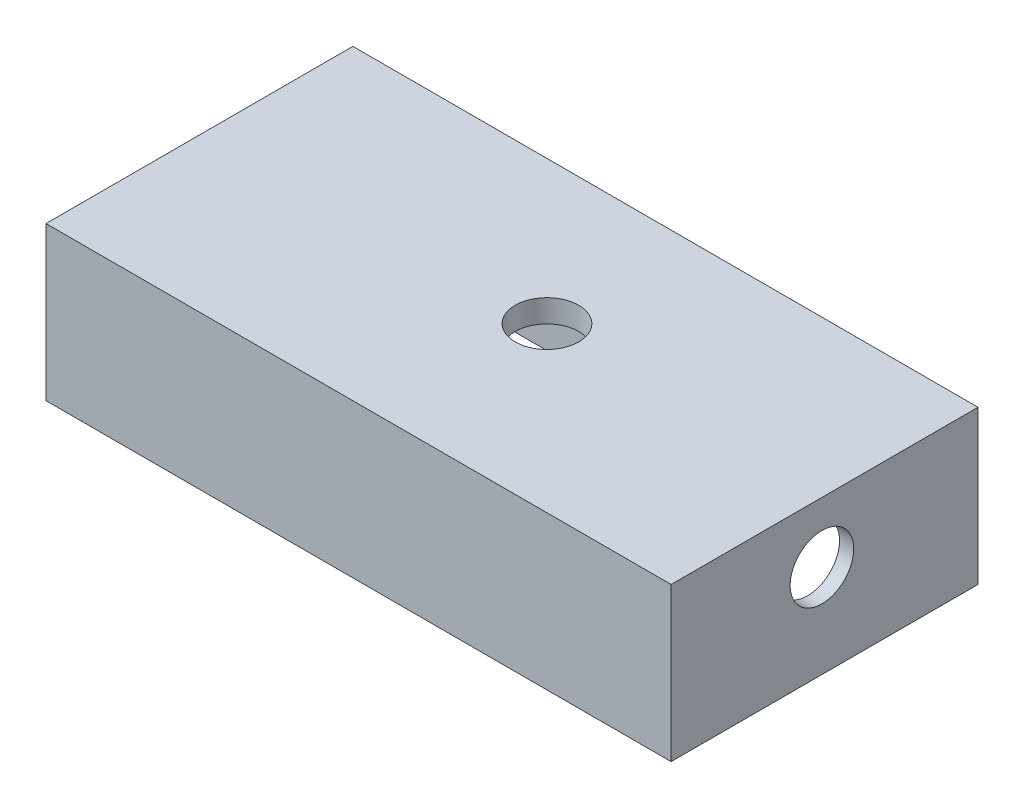
SolidWorks part; units mm, degrees
material "6061 Alloy"
ref_plane "Front Plane" through (0, 0, 0) normal (0, 0, 1) x (1, 0, 0)
ref_plane "Top Plane" through (0, 0, 0) normal (0, 1, 0) x (1, 0, 0)
ref_plane "Right Plane" through (0, 0, 0) normal (1, 0, 0) x (0, 0, -1)
sketch "Sketch1" plane through (0, 0, 0) normal (0, 1, 0) x (1, 0, 0)
  line L1 (-174.625, -85.725) -> (174.625, -85.725)
  line L2 (-174.625, -85.725) -> (-174.625, 85.725)
  line L3 (-174.625, 85.725) -> (174.625, 85.725)
  line L4 (174.625, -85.725) -> (174.625, 85.725)
  line L5 (-174.625, -85.725) -> (174.625, 85.725) construction
  line L6 (-174.625, 85.725) -> (174.625, -85.725) construction
  point P0 (0, 0)
  dimension "D1" = 349.25
  dimension "D2" = 171.45
extrude "Boss-Extrude1" add sketch "Sketch1" along normal blind 85.725
sketch "Sketch2" plane through (0, 0, 0) normal (0, -1, 0) x (1, 0, 0)
  line L0 (-143.1665, -77.8271) -> (-143.1665, -85.725) construction
  line L1 (174.625, -85.725) -> (-174.625, -85.725) construction
  line L2 (-166.7271, -54.2665) -> (-174.625, -54.2665) construction
  line L3 (-174.625, -85.725) -> (-174.625, 85.725) construction
  line L4 (143.1665, -77.8271) -> (143.1665, -85.725) construction
  line L5 (166.7271, -54.2665) -> (174.625, -54.2665) construction
  line L6 (174.625, 85.725) -> (174.625, -85.725) construction
  line L7 (-143.1665, 77.8271) -> (-143.1665, 85.725) construction
  line L8 (-174.625, 85.725) -> (174.625, 85.725) construction
  line L9 (-166.7271, 54.2665) -> (-174.625, 54.2665) construction
  line L10 (166.7271, 54.2665) -> (174.625, 54.2665) construction
  line L11 (143.1665, 77.8271) -> (143.1665, 85.725)
  line L18 (143.1665, 77.8271) -> (-143.1665, 77.8271)
  line L19 (166.7271, -54.2665) -> (166.7271, 54.2665)
  line L20 (-143.1665, -77.8271) -> (143.1665, -77.8271)
  line L21 (-166.7271, 54.2665) -> (-166.7271, -54.2665)
  arc A0 (166.7271, -54.2665) -> (143.1665, -77.8271) centre (143.1665, -54.2665) cw
  arc A1 (143.1665, 77.8271) -> (166.7271, 54.2665) centre (143.1665, 54.2665) cw
  arc A2 (-143.1665, 77.8271) -> (-166.7271, 54.2665) centre (-143.1665, 54.2665) ccw
  arc A3 (-143.1665, -77.8271) -> (-166.7271, -54.2665) centre (-143.1665, -54.2665) cw
  dimension "D2" = 23.5606
extrude "Cut-Extrude1" cut sketch "Sketch2" against normal offset from surface (73.025 mm away) 12.7 contours A1 L19 A0 L20 A3 L21 A2 L18 up to face at (0, 85.725, 0)
sketch "Sketch4" plane through (0, 73.025, 0) normal (0, -1, 0) x (1, 0, 0)
  line L0 (-166.7271, -6.35) -> (-166.7271, 6.35)
  line L2 (-166.7271, 54.2665) -> (-166.7271, -54.2665) construction
  line L3 (-166.7271, 6.35) -> (-64.0424, 6.35)
  line L4 (-64.0424, 6.35) -> (-64.0424, 77.8271)
  line L5 (-143.1665, 77.8271) -> (143.1665, 77.8271) construction
  line L6 (-64.0424, 77.8271) -> (-51.3424, 77.8271)
  line L7 (-51.3424, 77.8271) -> (-51.3424, 6.35)
  line L8 (-51.3424, 6.35) -> (51.3424, 6.35)
  line L9 (51.3424, 6.35) -> (51.3424, 77.8271)
  line L10 (51.3424, 77.8271) -> (64.0424, 77.8271)
  line L11 (64.0424, 77.8271) -> (64.0424, 6.35)
  line L12 (64.0424, 6.35) -> (166.7271, 6.35)
  line L13 (166.7271, 54.2665) -> (166.7271, -54.2665) construction
  line L14 (166.7271, 6.35) -> (166.7271, -6.35)
  line L15 (166.7271, -6.35) -> (64.0424, -6.35)
  line L16 (64.0424, -6.35) -> (64.0424, -77.8271)
  line L17 (143.1665, -77.8271) -> (-143.1665, -77.8271) construction
  line L18 (64.0424, -77.8271) -> (51.3424, -77.8271)
  line L19 (-143.1665, -77.8271) -> (143.1665, -77.8271) construction
  line L20 (51.3424, -77.8271) -> (51.3424, -6.35)
  line L21 (51.3424, -6.35) -> (-51.3424, -6.35)
  line L22 (-51.3424, -6.35) -> (-51.3424, -77.8271)
  line L23 (-51.3424, -77.8271) -> (-64.0424, -77.8271)
  line L24 (-64.0424, -77.8271) -> (-64.0424, -6.35)
  line L25 (-64.0424, -6.35) -> (-166.7271, -6.35)
  point P3 (-166.7271, 0)
  dimension "D1" = 12.7
extrude "Boss-Extrude3" [suppressed] add sketch "Sketch4" along normal blind 6.35
fillet "Fillet1" [suppressed] radius 19.05
sketch "Sketch5" plane through (0, 85.725, 0) normal (0, 1, 0) x (1, 0, 0)
  circle A0 centre (13.7243, 5.8112) radius 17.7497
  circle A1 centre (13.7243, 5.8112) radius 20.2897
  circle A2 centre (13.7243, 5.8112) radius 20.2897 construction
  dimension "D1" = 0
  dimension "D2" = 2.54
extrude "Cut-Extrude2" cut sketch "Sketch5" against normal up to next
sketch "Sketch6" plane through (174.625, 0, 0) normal (1, 0, 0) x (0, 0, -1)
  circle A0 centre (-1.4761, 51.9726) radius 17.7497
  circle A1 centre (-1.4761, 51.9726) radius 20.2897
  circle A2 centre (-1.4761, 51.9726) radius 20.2897 construction
  dimension "D1" = 0
  dimension "D2" = 2.54
extrude "Cut-Extrude3" cut sketch "Sketch6" against normal up to next
chamfer "Chamfer1" distance 0.635 8 edges at (159.8264, 0, -70.9264) (166.7271, 0, 0) (159.8264, 0, 70.9264) (0, 0, 77.8271) (-159.8264, 0, 70.9264) (0, 0, -77.8271) (-166.7271, 0, 0) (-159.8264, 0, -70.9264)
sketch "Sketch7" plane through (0, 0, 0) normal (0, -1, 0) x (1, 0, 0)
  line L0 (-174.625, -85.725) -> (-174.625, 85.725) construction
  line L1 (174.625, -85.725) -> (-174.625, -85.725) construction
  line L2 (174.625, 85.725) -> (174.625, -85.725) construction
  line L3 (-174.625, 85.725) -> (174.625, 85.725) construction
  line L4 (-174.625, -85.725) -> (-174.625, 85.725)
  line L5 (174.625, -85.725) -> (-174.625, -85.725)
  line L6 (174.625, 85.725) -> (174.625, -85.725)
  line L7 (-174.625, 85.725) -> (174.625, 85.725)
  line L36 (-130.175, -85.725) -> (-14.7855, -85.725)
  line L37 (-10.2954, -87.5849) -> (5.0349, -102.9151)
  line L38 (9.525, -104.775) -> (53.975, -104.775)
  line L39 (58.4651, -102.9151) -> (73.7954, -87.5849)
  line L40 (78.2855, -85.725) -> (149.225, -85.725)
  line L41 (153.7151, -87.5849) -> (169.0454, -102.9151)
  line L42 (173.5355, -104.775) -> (187.325, -104.775)
  line L43 (193.675, -98.425) -> (193.675, -53.975)
  line L44 (187.325, -47.625) -> (180.975, -47.625)
  line L45 (174.625, -41.275) -> (174.625, 41.275)
  line L46 (180.975, 47.625) -> (187.325, 47.625)
  line L47 (193.675, 53.975) -> (193.675, 98.425)
  line L48 (187.325, 104.775) -> (173.5355, 104.775)
  line L49 (169.0454, 102.9151) -> (153.7151, 87.5849)
  line L50 (149.225, 85.725) -> (78.2855, 85.725)
  line L51 (73.7954, 87.5849) -> (58.4651, 102.9151)
  line L52 (53.975, 104.775) -> (9.525, 104.775)
  line L53 (5.0349, 102.9151) -> (-10.2954, 87.5849)
  line L54 (-14.7855, 85.725) -> (-130.175, 85.725)
  line L55 (-136.525, 92.075) -> (-136.525, 98.425)
  line L56 (-142.875, 104.775) -> (-187.325, 104.775)
  line L57 (-193.675, 98.425) -> (-193.675, 53.975)
  line L58 (-187.325, 47.625) -> (-180.975, 47.625)
  line L59 (-174.625, 41.275) -> (-174.625, -41.275)
  line L60 (-180.975, -47.625) -> (-187.325, -47.625)
  line L61 (-193.675, -53.975) -> (-193.675, -98.425)
  line L62 (-187.325, -104.775) -> (-142.875, -104.775)
  line L63 (-136.525, -98.425) -> (-136.525, -92.075)
  line L64 (-130.175, -85.725) -> (-14.7855, -85.725)
  line L65 (-10.2954, -87.5849) -> (5.0349, -102.9151)
  line L66 (9.525, -104.775) -> (53.975, -104.775)
  line L67 (58.4651, -102.9151) -> (73.7954, -87.5849)
  line L68 (78.2855, -85.725) -> (149.225, -85.725)
  line L69 (153.7151, -87.5849) -> (169.0454, -102.9151)
  line L70 (173.5355, -104.775) -> (187.325, -104.775)
  line L71 (193.675, -98.425) -> (193.675, -53.975)
  line L72 (187.325, -47.625) -> (180.975, -47.625)
  line L73 (174.625, -41.275) -> (174.625, 41.275)
  line L74 (180.975, 47.625) -> (187.325, 47.625)
  line L75 (193.675, 53.975) -> (193.675, 98.425)
  line L76 (187.325, 104.775) -> (173.5355, 104.775)
  line L77 (169.0454, 102.9151) -> (153.7151, 87.5849)
  line L78 (149.225, 85.725) -> (78.2855, 85.725)
  line L79 (73.7954, 87.5849) -> (58.4651, 102.9151)
  line L80 (53.975, 104.775) -> (9.525, 104.775)
  line L81 (5.0349, 102.9151) -> (-10.2954, 87.5849)
  line L82 (-14.7855, 85.725) -> (-130.175, 85.725)
  line L83 (-136.525, 92.075) -> (-136.525, 98.425)
  line L84 (-142.875, 104.775) -> (-187.325, 104.775)
  line L85 (-193.675, 98.425) -> (-193.675, 53.975)
  line L86 (-187.325, 47.625) -> (-180.975, 47.625)
  line L87 (-174.625, 41.275) -> (-174.625, -41.275)
  line L88 (-180.975, -47.625) -> (-187.325, -47.625)
  line L89 (-193.675, -53.975) -> (-193.675, -98.425)
  line L90 (-187.325, -104.775) -> (-142.875, -104.775)
  line L91 (-136.525, -98.425) -> (-136.525, -92.075)
  circle A0 centre (12.7, 95.25) radius 3.2639 construction
  circle A1 centre (50.8, 95.25) radius 3.2639 construction
  circle A2 centre (184.15, 95.25) radius 3.2639 construction
  circle A3 centre (184.15, 57.15) radius 3.2639 construction
  circle A4 centre (184.15, -57.15) radius 3.2639 construction
  circle A5 centre (184.15, -95.25) radius 3.2639 construction
  circle A6 centre (50.8, -95.25) radius 3.2639 construction
  circle A7 centre (12.7, -95.25) radius 3.2639 construction
  circle A8 centre (-146.05, -95.25) radius 3.2639 construction
  circle A9 centre (-184.15, -95.25) radius 3.2639 construction
  circle A10 centre (-184.15, -57.15) radius 3.2639 construction
  circle A11 centre (-184.15, 57.15) radius 3.2639 construction
  circle A12 centre (-146.05, 95.25) radius 3.2639 construction
  circle A13 centre (-184.15, 95.25) radius 3.2639 construction
  circle A14 centre (12.7, 95.25) radius 3.2639
  circle A15 centre (50.8, 95.25) radius 3.2639
  circle A16 centre (184.15, 95.25) radius 3.2639
  circle A17 centre (184.15, 57.15) radius 3.2639
  circle A18 centre (184.15, -57.15) radius 3.2639
  circle A19 centre (184.15, -95.25) radius 3.2639
  circle A20 centre (50.8, -95.25) radius 3.2639
  circle A21 centre (12.7, -95.25) radius 3.2639
  circle A22 centre (-146.05, -95.25) radius 3.2639
  circle A23 centre (-184.15, -95.25) radius 3.2639
  circle A24 centre (-184.15, -57.15) radius 3.2639
  circle A25 centre (-184.15, 57.15) radius 3.2639
  circle A26 centre (-146.05, 95.25) radius 3.2639
  circle A27 centre (-184.15, 95.25) radius 3.2639
  arc A28 (-130.175, -85.725) -> (-136.525, -92.075) centre (-130.175, -92.075) ccw
  arc A29 (-10.2954, -87.5849) -> (-14.7855, -85.725) centre (-14.7855, -92.075) ccw
  arc A30 (5.0349, -102.9151) -> (9.525, -104.775) centre (9.525, -98.425) ccw
  arc A31 (53.975, -104.775) -> (58.4651, -102.9151) centre (53.975, -98.425) ccw
  arc A32 (78.2855, -85.725) -> (73.7954, -87.5849) centre (78.2855, -92.075) ccw
  arc A33 (153.7151, -87.5849) -> (149.225, -85.725) centre (149.225, -92.075) ccw
  arc A34 (169.0454, -102.9151) -> (173.5355, -104.775) centre (173.5355, -98.425) ccw
  arc A35 (187.325, -104.775) -> (193.675, -98.425) centre (187.325, -98.425) ccw
  arc A36 (193.675, -53.975) -> (187.325, -47.625) centre (187.325, -53.975) ccw
  arc A37 (174.625, -41.275) -> (180.975, -47.625) centre (180.975, -41.275) ccw
  arc A38 (180.975, 47.625) -> (174.625, 41.275) centre (180.975, 41.275) ccw
  arc A39 (187.325, 47.625) -> (193.675, 53.975) centre (187.325, 53.975) ccw
  arc A40 (193.675, 98.425) -> (187.325, 104.775) centre (187.325, 98.425) ccw
  arc A41 (173.5355, 104.775) -> (169.0454, 102.9151) centre (173.5355, 98.425) ccw
  arc A42 (149.225, 85.725) -> (153.7151, 87.5849) centre (149.225, 92.075) ccw
  arc A43 (73.7954, 87.5849) -> (78.2855, 85.725) centre (78.2855, 92.075) ccw
  arc A44 (58.4651, 102.9151) -> (53.975, 104.775) centre (53.975, 98.425) ccw
  arc A45 (9.525, 104.775) -> (5.0349, 102.9151) centre (9.525, 98.425) ccw
  arc A46 (-14.7855, 85.725) -> (-10.2954, 87.5849) centre (-14.7855, 92.075) ccw
  arc A47 (-136.525, 92.075) -> (-130.175, 85.725) centre (-130.175, 92.075) ccw
  arc A48 (-136.525, 98.425) -> (-142.875, 104.775) centre (-142.875, 98.425) ccw
  arc A49 (-187.325, 104.775) -> (-193.675, 98.425) centre (-187.325, 98.425) ccw
  arc A50 (-193.675, 53.975) -> (-187.325, 47.625) centre (-187.325, 53.975) ccw
  arc A51 (-174.625, 41.275) -> (-180.975, 47.625) centre (-180.975, 41.275) ccw
  arc A52 (-180.975, -47.625) -> (-174.625, -41.275) centre (-180.975, -41.275) ccw
  arc A53 (-187.325, -47.625) -> (-193.675, -53.975) centre (-187.325, -53.975) ccw
  arc A54 (-193.675, -98.425) -> (-187.325, -104.775) centre (-187.325, -98.425) ccw
  arc A55 (-142.875, -104.775) -> (-136.525, -98.425) centre (-142.875, -98.425) ccw
  arc A56 (-130.175, -85.725) -> (-136.525, -92.075) centre (-130.175, -92.075) ccw
  arc A57 (-10.2954, -87.5849) -> (-14.7855, -85.725) centre (-14.7855, -92.075) ccw
  arc A58 (5.0349, -102.9151) -> (9.525, -104.775) centre (9.525, -98.425) ccw
  arc A59 (53.975, -104.775) -> (58.4651, -102.9151) centre (53.975, -98.425) ccw
  arc A60 (78.2855, -85.725) -> (73.7954, -87.5849) centre (78.2855, -92.075) ccw
  arc A61 (153.7151, -87.5849) -> (149.225, -85.725) centre (149.225, -92.075) ccw
  arc A62 (169.0454, -102.9151) -> (173.5355, -104.775) centre (173.5355, -98.425) ccw
  arc A63 (187.325, -104.775) -> (193.675, -98.425) centre (187.325, -98.425) ccw
  arc A64 (193.675, -53.975) -> (187.325, -47.625) centre (187.325, -53.975) ccw
  arc A65 (174.625, -41.275) -> (180.975, -47.625) centre (180.975, -41.275) ccw
  arc A66 (180.975, 47.625) -> (174.625, 41.275) centre (180.975, 41.275) ccw
  arc A67 (187.325, 47.625) -> (193.675, 53.975) centre (187.325, 53.975) ccw
  arc A68 (193.675, 98.425) -> (187.325, 104.775) centre (187.325, 98.425) ccw
  arc A69 (173.5355, 104.775) -> (169.0454, 102.9151) centre (173.5355, 98.425) ccw
  arc A70 (149.225, 85.725) -> (153.7151, 87.5849) centre (149.225, 92.075) ccw
  arc A71 (73.7954, 87.5849) -> (78.2855, 85.725) centre (78.2855, 92.075) ccw
  arc A72 (58.4651, 102.9151) -> (53.975, 104.775) centre (53.975, 98.425) ccw
  arc A73 (9.525, 104.775) -> (5.0349, 102.9151) centre (9.525, 98.425) ccw
  arc A74 (-14.7855, 85.725) -> (-10.2954, 87.5849) centre (-14.7855, 92.075) ccw
  arc A75 (-136.525, 92.075) -> (-130.175, 85.725) centre (-130.175, 92.075) ccw
  arc A76 (-136.525, 98.425) -> (-142.875, 104.775) centre (-142.875, 98.425) ccw
  arc A77 (-187.325, 104.775) -> (-193.675, 98.425) centre (-187.325, 98.425) ccw
  arc A78 (-193.675, 53.975) -> (-187.325, 47.625) centre (-187.325, 53.975) ccw
  arc A79 (-174.625, 41.275) -> (-180.975, 47.625) centre (-180.975, 41.275) ccw
  arc A80 (-180.975, -47.625) -> (-174.625, -41.275) centre (-180.975, -41.275) ccw
  arc A81 (-187.325, -47.625) -> (-193.675, -53.975) centre (-187.325, -53.975) ccw
  arc A82 (-193.675, -98.425) -> (-187.325, -104.775) centre (-187.325, -98.425) ccw
  arc A83 (-142.875, -104.775) -> (-136.525, -98.425) centre (-142.875, -98.425) ccw
  line M69 (174.625, -85.725) -> (174.625, 85.725)
  line M70 (174.625, 85.725) -> (-174.625, 85.725)
  line M71 (-174.625, 85.725) -> (-174.625, -85.725)
  line M72 (-174.625, -85.725) -> (174.625, -85.725)
  dimension "D1" = 0
extrude "Boss-Extrude4" [suppressed] add sketch "Sketch7" against normal blind 6.35 contours A79 A75 L83 A76 L84 A77 L85 A78 L86 A27 A26 A25 M71 M70 | A74 A71 L79 A72 L80 A73 L81 A14 A15 M70 | A70 A66 L74 A67 L75 A68 L76 A69 L77 A17 A16 M70 M69 | A65 A61 L69 A62 L70 A63 L71 A64 L72 A18 A19 M69 M72 | A60 A57 L65 A58 L66 A59 L67 A21 A20 M72 | L90 A83 L91 A56 A80 L88 A81 L89 A82 A24 A23 A22 M72 M71
equation "\"oring.277.ID\"= 11.484in"
equation "\"oring.277.A\"= 11.750in"
equation "\"oring.277.A1\"= 11.722in"
equation "\"oring.277.B\"= 11.500in"
equation "\"oring.277.B1\"= 11.528in"
equation "\"oring.277.C\"= 11.747in"
equation "\"oring.277.D\"= 11.503in"
equation "\"oring.277.G\"= 0.187in"
equation "\"D1@Sketch2\"=(\"oring.277.A\"+\"anodize.add\"*2)*PI"
equation "\"D2@Sketch2\"=6 * \"oring.277.W\" +(\"oring.277.C.factor\" - \"oring.277.B1\")/2"
equation "\"oring.277.W\"= 0.139in"
equation "\"anodize.add\"= 0.001in"
equation "\"c.factor\"= 0.00271"
equation "\"oring.277.C.factor\"= \"oring.277.C\" - \"oring.277.C\" * \"c.factor\""
